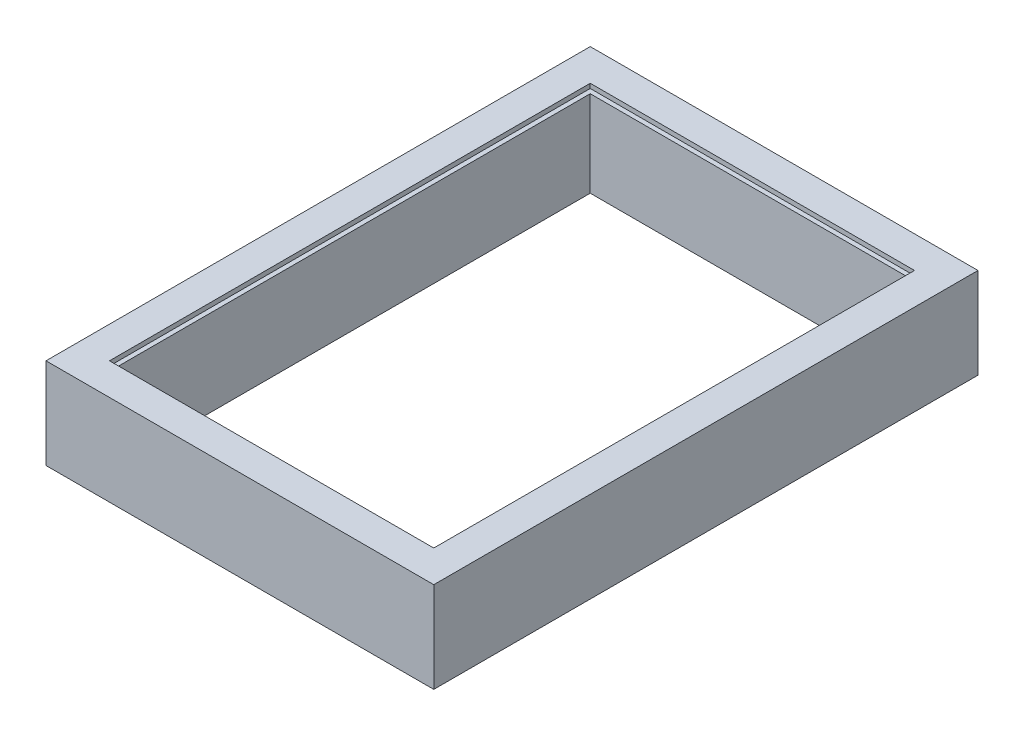
SolidWorks part; units mm, degrees
ref_plane "Спереди" through (0, 0, 0) normal (0, 0, 1) x (1, 0, 0)
ref_plane "Сверху" through (0, 0, 0) normal (0, 1, 0) x (1, 0, 0)
ref_plane "Справа" through (0, 0, 0) normal (1, 0, 0) x (0, 0, -1)
sketch "Эскиз1" plane through (0, 0, 0) normal (0, 1, 0) x (1, 0, 0)
  line L1 (-347.5, 520) -> (347.5, 520)
  line L2 (-347.5, 520) -> (-347.5, -520)
  line L3 (-347.5, -520) -> (347.5, -520)
  line L4 (347.5, 520) -> (347.5, -520)
  line L5 (-347.5, 520) -> (347.5, -520) construction
  line L6 (-347.5, -520) -> (347.5, 520) construction
  point P0 (0, 0)
extrude "Вытянуть-Тонкостенный1" add sketch "Эскиз1" along normal blind 200 thin thin type one direction wall 80
sketch "Эскиз2" plane through (0, 200, 0) normal (0, 1, 0) x (1, 0, 0)
  line L0 (347.5, 520) -> (-347.5, 520) construction
  line L1 (-357.5, 530) -> (357.5, 530)
  line L2 (-357.5, 530) -> (-357.5, -530)
  line L3 (-357.5, -530) -> (357.5, -530)
  line L4 (357.5, 530) -> (357.5, -530)
  line L5 (-347.5, -520) -> (347.5, -520) construction
  line L6 (347.5, -520) -> (347.5, 520) construction
  line L7 (-347.5, 520) -> (-347.5, -520) construction
  point P4 (0, 0)
  point P6 (0, 0)
  point P7 (356.2936, -554.3592)
  point P9 (0, 0)
  dimension "D1" = 10
  dimension "D2" = 10
  dimension "D3" = 10
  dimension "D4" = 10
extrude "Вырез-Вытянуть1" cut sketch "Эскиз2" against normal blind 10
